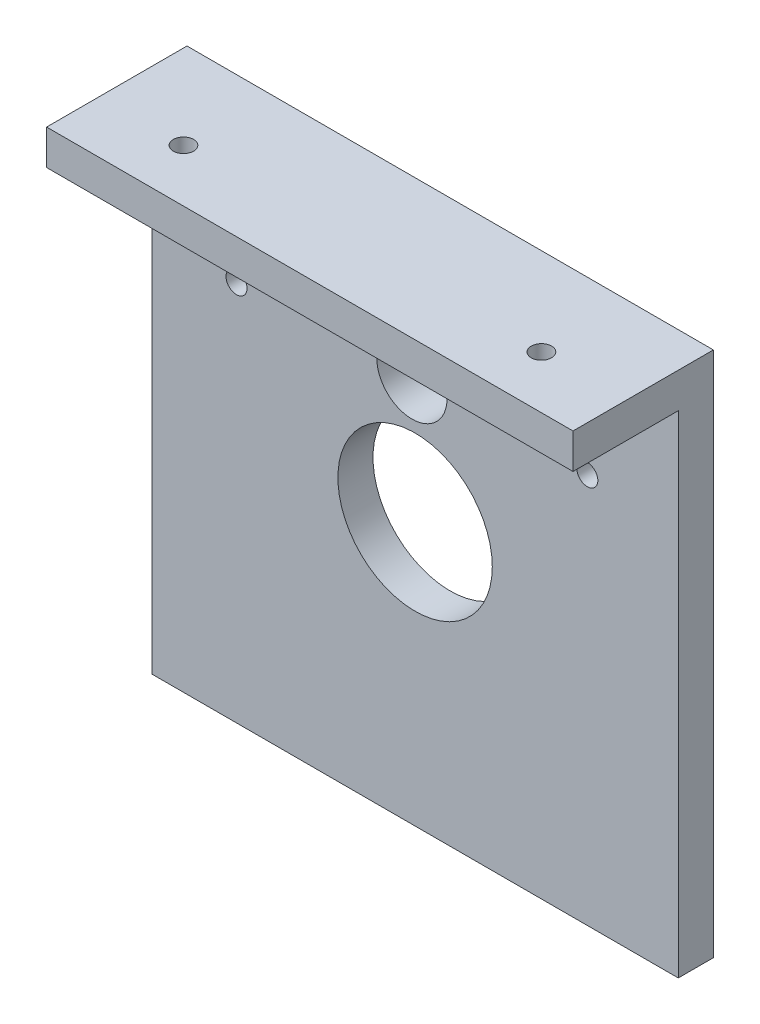
SolidWorks part; units mm, degrees
ref_plane "Ön Düzlem" through (0, 0, 0) normal (0, 0, 1) x (1, 0, 0)
ref_plane "Üst Düzlem" through (0, 0, 0) normal (0, 1, 0) x (1, 0, 0)
ref_plane "Sağ Düzlem" through (0, 0, 0) normal (1, 0, 0) x (0, 0, -1)
sketch "Sketch1" plane through (0, 0, 0) normal (0, 0, 1) x (1, 0, 0)
  line L0 (-35.6377, -29.993) -> (39.3623, -29.993)
  line L1 (-35.6377, 45.007) -> (39.3623, 45.007)
  line L2 (-35.6377, 45.007) -> (-35.6377, -29.993)
  line L3 (-35.6377, 45.007) -> (39.3623, -29.993) construction
  line L4 (39.3623, 45.007) -> (39.3623, -29.993)
  line L5 (39.3623, 45.007) -> (-35.6377, -29.993) construction
  circle A0 centre (1.8623, 7.507) radius 11
  circle A1 centre (1.4091, 25.0012) radius 5
  circle A2 centre (-23.5825, 24.3539) radius 1.5
  circle A3 centre (26.4008, 25.6485) radius 1.5
  point P0 (0, 0)
  dimension "D2" = 22
  dimension "D3" = 10
  dimension "D5" = 3
  dimension "D6" = 3
  dimension "D1" = 75
  dimension "D4" = 17.5
  dimension "D7" = 50
  dimension "D8" = 25
  dimension "D9" = 75
  dimension "D10" = 75
extrude "Boss-Extrude1" add sketch "Sketch1" along normal blind 5
sketch "Sketch3" plane through (0, 0, 5) normal (0, 0, 1) x (1, 0, 0)
  line L0 (39.3623, -29.993) -> (39.3623, 45.007) construction
  line L1 (-35.6377, 45.007) -> (39.3623, 45.007)
  line L2 (-35.6377, 45.007) -> (-35.6377, 40.007)
  line L3 (-35.6377, 40.007) -> (39.3623, 40.007)
  line L4 (39.3623, 45.007) -> (39.3623, 40.007)
  dimension "D1" = 5
extrude "Boss-Extrude2" add sketch "Sketch3" along normal blind 15
hole_wizard "CSK for M2.5 Flat Head Machine Screw1" positions "Sketch5" profile "Sketch4" countersink size "M2.5" standard "ANSI Metric" end condition through all
sketch "Sketch5" plane through (0, 40.007, 0) normal (0, -1, 0) x (-1, 0, 0)
  line L0 (-39.3623, -20) -> (-39.3623, -5) construction
  line L2 (35.6377, -20) -> (-39.3623, -20) construction
  line L3 (35.6377, -5) -> (-39.3623, -5) construction
  line L4 (35.6377, -20) -> (35.6377, -5) construction
  point P0 (-27.3623, -12.5)
  point P2 (23.6377, -12.5)
  dimension "D1" = 12
  dimension "D2" = 7.5
  dimension "D3" = 7.5
  dimension "D4" = 12
sketch "Sketch4" plane through (27.3623, 40.007, 12.5) normal (1, 0, 0) x (0, 0, -1)
  line L0 (0, 0) -> (0, 5)
  line L1 (0, 5) -> (1.45, 5)
  line L2 (1.45, 5) -> (1.45, 1.3)
  line L3 (1.45, 1.3) -> (2.75, 0)
  line L5 (2.75, 0) -> (0, 0)
  line L6 (-1.45, 1.3) -> (-2.75, 0) construction
  line L11 (0, -6.35) -> (0, 107.95) construction
  dimension "Thru Hole Dia." = 2.9
  dimension "Thru Hole Depth" = 5
  dimension "Near C'Sink Dia." = 5.5
  dimension "Near C'Sink Angle" = 90
